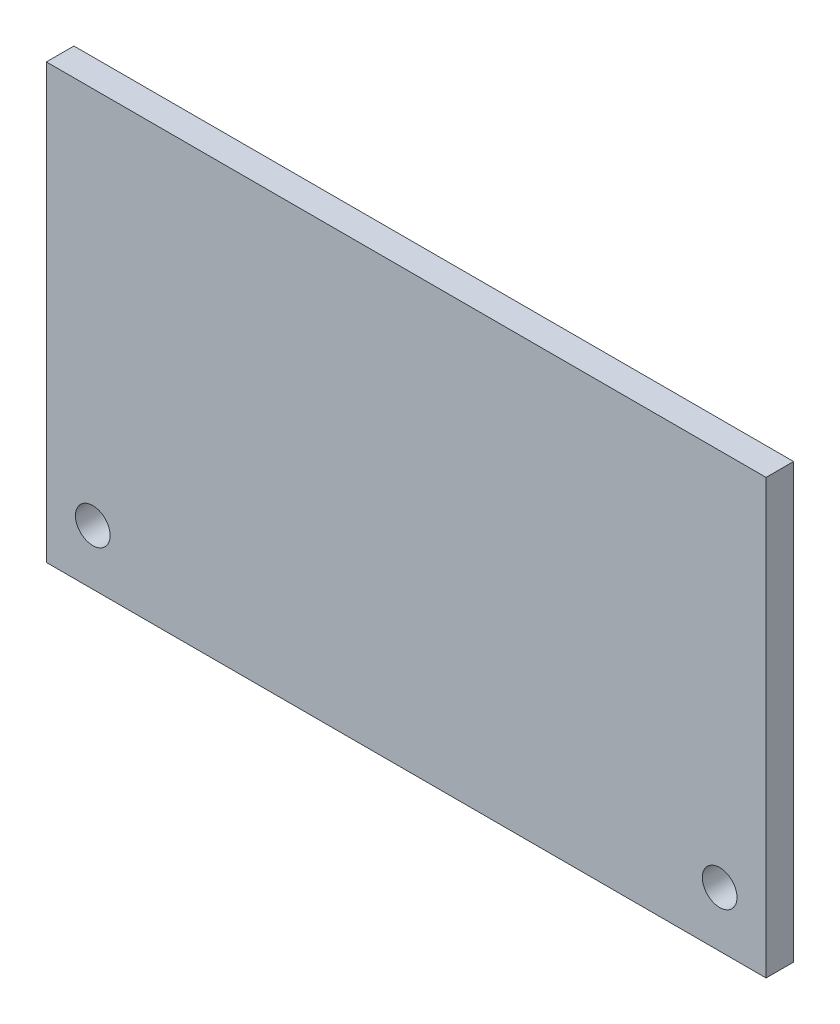
SolidWorks part; units mm, degrees
ref_plane "Front Plane" through (0, 0, 0) normal (0, 0, 1) x (1, 0, 0)
ref_plane "Top Plane" through (0, 0, 0) normal (0, 1, 0) x (1, 0, 0)
ref_plane "Right Plane" through (0, 0, 0) normal (1, 0, 0) x (0, 0, -1)
sketch "Sketch1" plane through (0, 0, 0) normal (0, 0, 1) x (1, 0, 0)
  line L1 (-83, 50) -> (83, 50)
  line L2 (-83, 50) -> (-83, -50)
  line L3 (-83, -50) -> (83, -50)
  line L4 (83, 50) -> (83, -50)
  line L5 (-83, 50) -> (83, -50) construction
  line L6 (-83, -50) -> (83, 50) construction
  point P0 (0, 0)
  dimension "D1" = 100
  dimension "D2" = 166
extrude "Boss-Extrude1" add sketch "Sketch1" along normal blind 6.35
sketch "Sketch2" plane through (0, 0, 6.35) normal (0, 0, 1) x (1, 0, 0)
  line L0 (-83, -50) -> (83, -50) construction
  line L1 (83, -50) -> (83, 50) construction
  line L2 (-83, 50) -> (-83, -50) construction
  circle A0 centre (-72.3, -37.27) radius 4
  circle A1 centre (72.3, -37.27) radius 4
  dimension "D1" = 8
  dimension "D2" = 12.73
  dimension "D3" = 10.7
  dimension "D4" = 10.7
extrude "Cut-Extrude1" cut sketch "Sketch2" against normal blind 6.35
